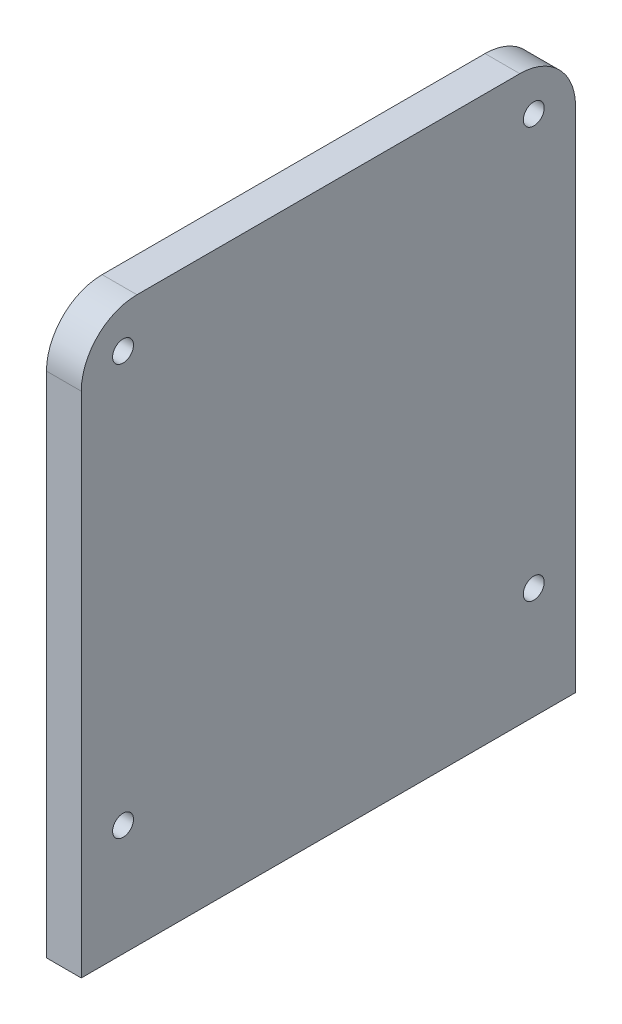
SolidWorks part; units mm, degrees
ref_plane "Front Plane" through (0, 0, 0) normal (0, 0, 1) x (1, 0, 0)
ref_plane "Top Plane" through (0, 0, 0) normal (0, 1, 0) x (1, 0, 0)
ref_plane "Right Plane" through (0, 0, 0) normal (1, 0, 0) x (0, 0, -1)
sketch "Sketch1" plane through (0, 0, 0) normal (1, 0, 0) x (0, 0, -1)
  line L1 (0, 0) -> (71, 0)
  line L2 (0, 0) -> (0, 81)
  line L3 (0, 81) -> (71, 81)
  line L4 (71, 0) -> (71, 81)
  circle A0 centre (6, 75) radius 1.5
  circle A1 centre (65, 75) radius 1.5
  circle A2 centre (6, 16) radius 1.5
  circle A3 centre (65, 16) radius 1.5
  dimension "D4" = 3
  dimension "D1" = 71
  dimension "D2" = 81
  dimension "D3" = 59
  dimension "D5" = 6
  dimension "D6" = 6
  dimension "D7" = 59
extrude "Boss-Extrude1" add sketch "Sketch1" along normal blind 5
fillet "Fillet1" radius 8 2 edges at (2.5, 81, -71) (2.5, 81, 0)
